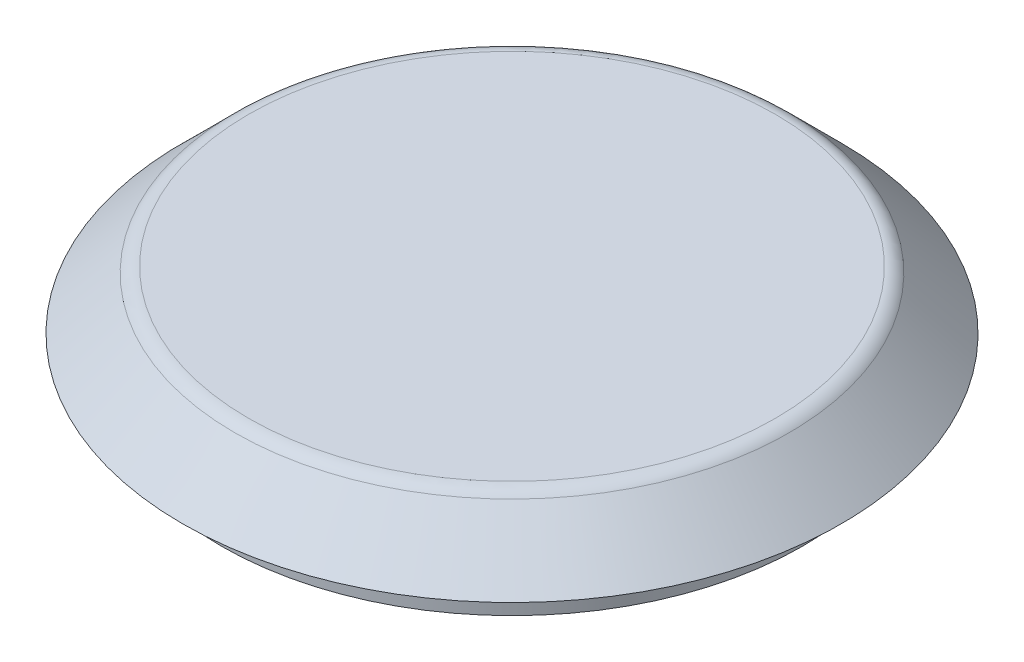
SolidWorks part; units mm, degrees
ref_plane "Front Plane" through (0, 0, 0) normal (0, 0, 1) x (1, 0, 0)
ref_plane "Top Plane" through (0, 0, 0) normal (0, 1, 0) x (1, 0, 0)
ref_plane "Right Plane" through (0, 0, 0) normal (1, 0, 0) x (0, 0, -1)
sketch "Sketch2" plane through (0, 0, 0) normal (0, 0, 1) x (1, 0, 0)
  line L0 (15, 0) -> (15, 2)
  line L1 (15, 2) -> (17, 2)
  line L2 (17, 2) -> (14.2929, 4.7071)
  line L3 (13.5858, 5) -> (0, 5)
  line L4 (0, 5) -> (0, 0)
  line L5 (0, 0) -> (15, 0)
  arc A0 (14.2929, 4.7071) -> (13.5858, 5) centre (13.5858, 4) ccw
  dimension "D6" = 1
  dimension "D1" = 17
  dimension "D2" = 15
  dimension "D3" = 5
  dimension "D4" = 2
  dimension "D5" = 45
revolve "Revolve1" add sketch "Sketch2" angle 360 about L4
shell "Shell1" thickness 1
